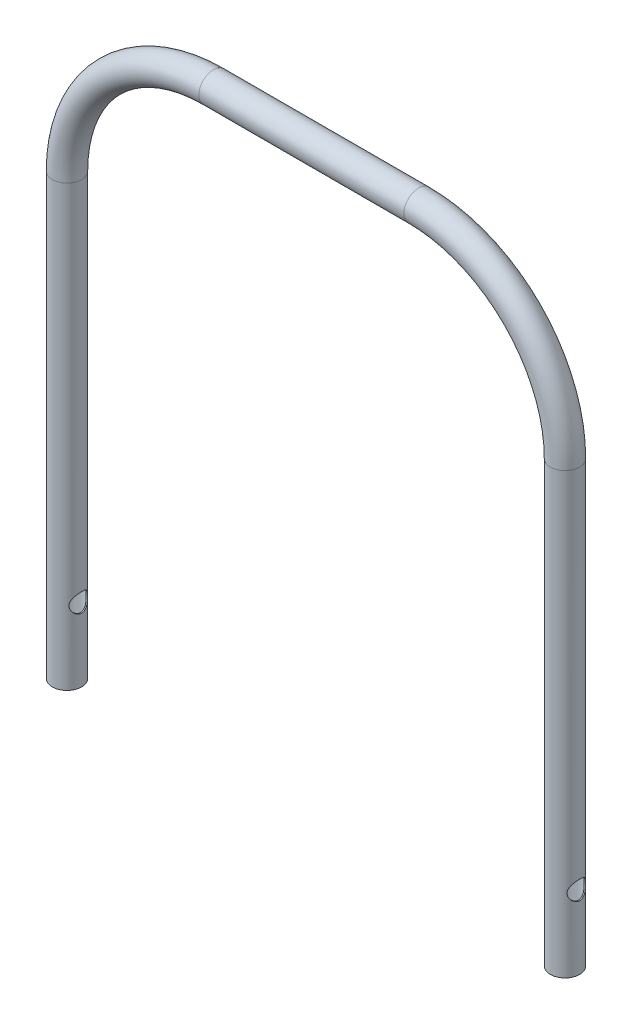
SolidWorks part; units mm, degrees
material "6063-T1"
ref_plane "Front Plane" through (0, 0, 0) normal (0, 0, 1) x (1, 0, 0)
ref_plane "Top Plane" through (0, 0, 0) normal (0, 1, 0) x (1, 0, 0)
ref_plane "Right Plane" through (0, 0, 0) normal (1, 0, 0) x (0, 0, -1)
sketch "Centerline" plane through (0, 0, 0) normal (0, 0, 1) x (1, 0, 0)
  line L0 (0, 0) -> (0, 300)
  line L5 (0, 300) -> (-100, 300) construction
  line L6 (-100, 300) -> (-100, 400) construction
  line L7 (0, 0) -> (-340, 0) construction
  line L8 (-170, 0) -> (-170, 565.0483) construction
  line L9 (-100, 400) -> (-240, 400)
  line L10 (-340, 0) -> (-340, 300)
  arc A2 (0, 300) -> (-100, 400) centre (-100, 300) ccw
  arc A3 (-340, 300) -> (-240, 400) centre (-240, 300) cw
  point P11 (-170, 400)
  dimension "D3" = 340
  dimension "D1" = 100
  dimension "D2" = 300
ref_plane "Plane2" through (-400, 0, 0) normal (1, 0, 0) x (0, 0, -1)
other "Round_tube DO20_DI18_5(1)"
ref_plane "Plane3" through (0, 0, 0) normal (0, 1, 0) x (-1, 0, 0)
sketch "Sketch1" plane through (0, 0, 0) normal (0, 1, 0) x (-1, 0, 0)
  circle A0 centre (0, 0) radius 9.25
  circle A1 centre (0, 0) radius 10
  point P4 (0, 0)
  dimension "D1" = 20
  dimension "D2" = 18.5
sketch "Sketch2" plane through (-400, 0, 0) normal (1, 0, 0) x (0, 0, -1)
  line L0 (0, 0) -> (0, 130.2046) construction
hole_wizard "Ø12.0mm Dowel Hole2" positions "Sketch5" profile "Sketch6" hole size "Ø12.0" standard "ANSI Metric" end condition through all
sketch "Sketch5" plane through (-400, 0, 0) normal (1, 0, 0) x (0, 0, -1)
  point P0 (0, 50)
  dimension "D1" = 50
sketch "Sketch6" plane through (-400, 50, 0) normal (0, 1, 0) x (0, 0, 1)
  line L0 (0, 0) -> (0, 410)
  line L1 (0, 410) -> (6.35, 410)
  line L2 (6.35, 410) -> (6.35, 0)
  line L5 (6.35, 0) -> (0, 0)
  line L11 (0, -6.35) -> (0, 107.95) construction
  dimension "Thru Hole Dia." = 12.7
  dimension "Thru Hole Depth" = 410
